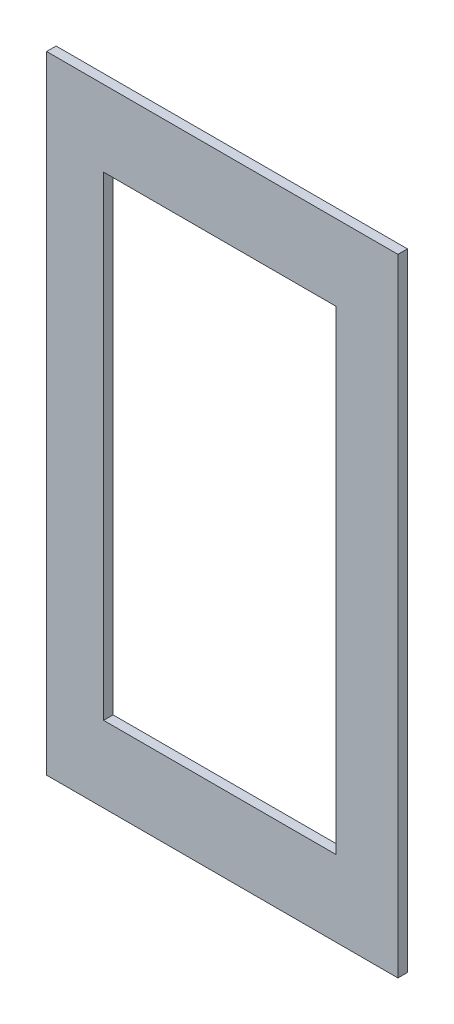
SolidWorks part; units mm, degrees
ref_plane "Alzado" through (0, 0, 0) normal (0, 0, 1) x (1, 0, 0)
ref_plane "Planta" through (0, 0, 0) normal (0, 1, 0) x (1, 0, 0)
ref_plane "Vista lateral" through (0, 0, 0) normal (1, 0, 0) x (0, 0, -1)
sketch "Croquis2" plane through (0, 0, 0) normal (0, 1, 0) x (1, 0, 0)
  line L1 (-117.475, 3.175) -> (117.475, 3.175)
  line L2 (-117.475, 3.175) -> (-117.475, -3.175)
  line L3 (-117.475, -3.175) -> (117.475, -3.175)
  line L4 (117.475, 3.175) -> (117.475, -3.175)
  line L5 (-117.475, 3.175) -> (117.475, -3.175) construction
  line L6 (-117.475, -3.175) -> (117.475, 3.175) construction
  point P0 (0, 0)
  dimension "D1" = 234.95
  dimension "D2" = 6.35
extrude "Saliente-Extruir1" add sketch "Croquis2" along normal blind 419.1
sketch "Croquis7" plane through (0, 0, 3.175) normal (0, 0, 1) x (1, 0, 0)
  line L0 (-117.475, 191.2552) -> (-79.375, 191.2552) construction
  line L1 (-117.475, 338.2974) -> (-79.375, 338.2974) construction
  line L3 (-117.475, 419.1) -> (-117.475, 0) construction
  line L4 (67.9232, 0) -> (67.9232, 50.8) construction
  line L5 (-117.475, 0) -> (117.475, 0) construction
  line L6 (117.475, 125.3703) -> (79.375, 125.3703) construction
  line L7 (117.475, 419.1) -> (117.475, 0) construction
  line L9 (-79.375, 368.3) -> (76.2, 368.3)
  line L10 (-79.375, 368.3) -> (-79.375, 50.8)
  line L11 (-79.375, 50.8) -> (76.2, 50.8)
  line L12 (76.2, 368.3) -> (76.2, 50.8)
  dimension "D1" = 50.8
  dimension "D2" = 38.1
  dimension "D3" = 50.8
  dimension "D4" = 38.1
  dimension "D5" = 38.1
extrude "Cortar-Extruir3" cut sketch "Croquis7" against normal blind 6.35
